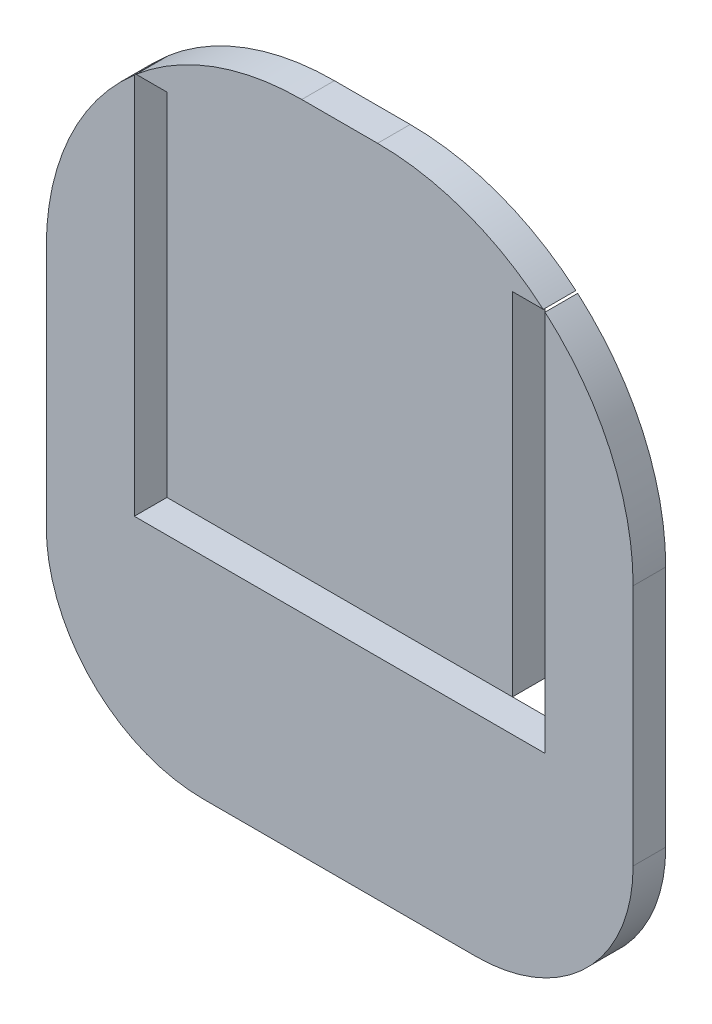
SolidWorks part; units mm, degrees
ref_plane "Front Plane" through (0, 0, 0) normal (0, 0, 1) x (1, 0, 0)
ref_plane "Top Plane" through (0, 0, 0) normal (0, 1, 0) x (1, 0, 0)
ref_plane "Right Plane" through (0, 0, 0) normal (1, 0, 0) x (0, 0, -1)
sketch "Sketch1" plane through (0, 0, 0) normal (0, 0, 1) x (1, 0, 0)
  line L0 (0, 8.5) -> (0, -86.5) construction
  line L1 (-43, 8.5) -> (43, 8.5) construction
  line L2 (-43, 8.5) -> (-43, -86.5) construction
  line L3 (-43, -86.5) -> (43, -86.5) construction
  line L4 (43, 8.5) -> (43, -86.5) construction
  line L5 (-5, 8.5) -> (5, 8.5) construction
  line L6 (-18, -86.5) -> (18, -86.5) construction
  line L7 (-43, -29.5) -> (43, -29.5) construction
  line L8 (-43, -29.5) -> (-43, -61.5) construction
  line L9 (-43, -61.5) -> (43, -61.5) construction
  line L10 (43, -29.5) -> (43, -61.5) construction
  line L11 (-0.5, -86.5) -> (0.5, -86.5) construction
  line L12 (-18, -86.5) -> (-0.5, -86.5) construction
  line L13 (0.5, -86.5) -> (18, -86.5) construction
  line L14 (-0.5, -86.5) -> (0.5, -86.5) construction
  line L15 (-18, -82.2) -> (-0.5, -82.2)
  line L16 (-0.5, -82.2) -> (0.5, -82.2)
  line L17 (0.5, -82.2) -> (18, -82.2)
  line L18 (38.7, -29.5) -> (38.7, -61.5)
  line L19 (-5, 4.2) -> (5, 4.2)
  line L20 (-38.7, -29.5) -> (-38.7, -61.5)
  arc A0 (-43, -29.5) -> (-5, 8.5) centre (-5, -29.5) cw construction
  arc A1 (5, 8.5) -> (43, -29.5) centre (5, -29.5) cw construction
  arc A2 (-43, -61.5) -> (-18, -86.5) centre (-18, -61.5) ccw construction
  arc A3 (18, -86.5) -> (43, -61.5) centre (18, -61.5) ccw construction
  arc A4 (18, -82.2) -> (38.7, -61.5) centre (18, -61.5) ccw
  arc A5 (5, 4.2) -> (38.7, -29.5) centre (5, -29.5) cw
  arc A6 (-38.7, -29.5) -> (-5, 4.2) centre (-5, -29.5) cw
  arc A7 (-38.7, -61.5) -> (-18, -82.2) centre (-18, -61.5) ccw
  point P10 (0, 8.5)
  point P19 (0, -86.5)
  point P23 (0, -86.5)
  dimension "D3" = 25
  dimension "D4" = 38
  dimension "D1" = 95
  dimension "D2" = 86
  dimension "D5" = 1
  dimension "D6" = 29.5
  dimension "D7" = 4.3
extrude "Boss-Extrude1" add sketch "Sketch1" along normal blind 4.3
sketch "Sketch2" plane through (0, 0, 4.3) normal (0, 0, 1) x (1, 0, 0)
  line L0 (-27.085, -4.0453) -> (-27.085, -3.8453)
  line L1 (-27.085, -4.0453) -> (-22.785, -4.0453) construction
  line L2 (-27.085, -4.0453) -> (-27.085, -54.4453)
  line L3 (-27.085, -54.4453) -> (27.085, -54.4453)
  line L4 (27.085, -4.0453) -> (27.085, -54.4453)
  line L5 (-27.085, -3.8453) -> (-22.785, -3.8453)
  line L6 (27.085, -3.8453) -> (27.085, -4.0453)
  line L7 (-22.785, -3.8453) -> (-22.785, -50.1453)
  line L8 (-22.785, -50.1453) -> (22.785, -50.1453)
  line L9 (22.785, -50.1453) -> (22.785, -3.8453)
  line L10 (-22.785, -3.8453) -> (22.785, -3.8453) construction
  line L11 (22.785, -3.8453) -> (27.085, -3.8453)
  line L12 (-22.785, -4.0453) -> (22.785, -4.0453) construction
  line L13 (22.785, -4.0453) -> (27.085, -4.0453) construction
  arc A1 (-5, 4.2) -> (-38.7, -29.5) centre (-5, -29.5) ccw construction
  dimension "D1" = 54.17
  dimension "D2" = 50.4
  dimension "D3" = 4.3
  dimension "D4" = 4.3
  dimension "D5" = 4.3
  dimension "D6" = 0.2
extrude "Cut-Extrude1" cut sketch "Sketch2" against normal blind 10
equation "\"D4@Sketch2\"=\"D3@Sketch2\""
equation "\"D5@Sketch2\"=\"D3@Sketch2\""
